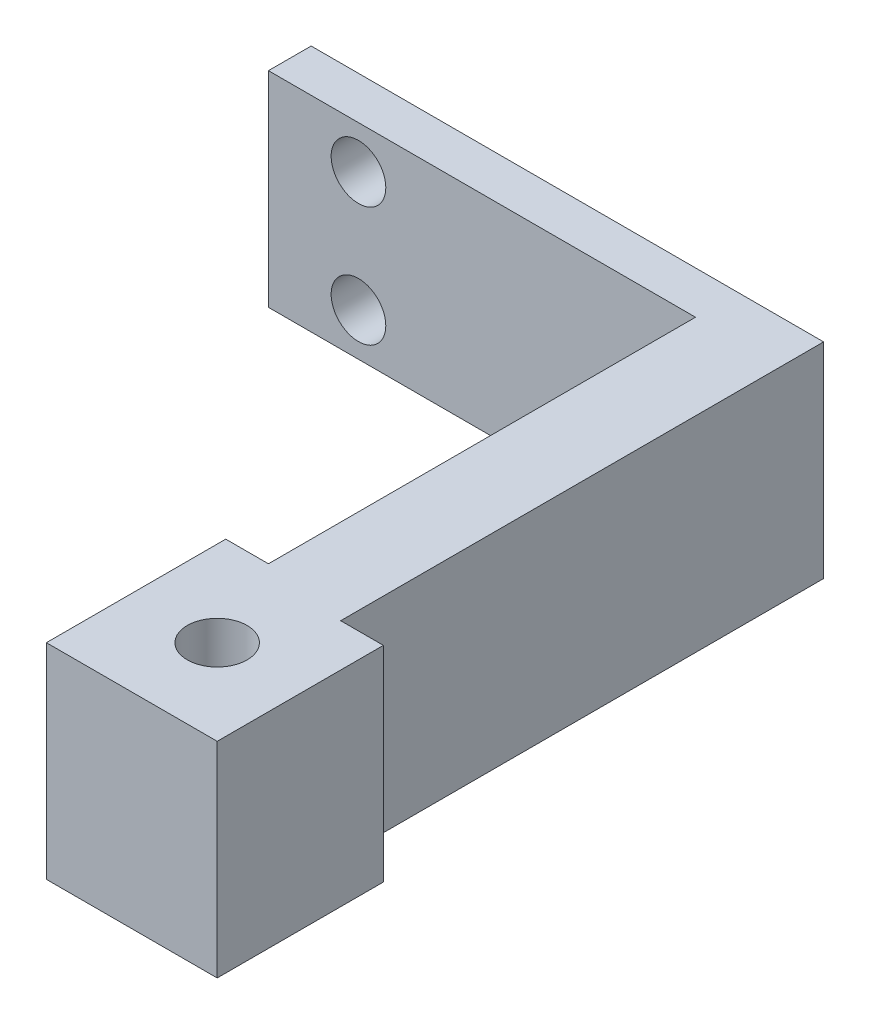
SolidWorks part; units mm, degrees
ref_plane "Front Plane" through (0, 0, 0) normal (0, 0, 1) x (1, 0, 0)
ref_plane "Top Plane" through (0, 0, 0) normal (0, 1, 0) x (1, 0, 0)
ref_plane "Right Plane" through (0, 0, 0) normal (1, 0, 0) x (0, 0, -1)
sketch "Sketch1" plane through (0, 0, 0) normal (0, 1, 0) x (1, 0, 0)
  line L0 (-1.6496, 29.2913) -> (-1.6496, -3.7087)
  line L1 (-1.6496, -3.7087) -> (3.3504, -3.7087)
  line L2 (3.3504, -3.7087) -> (3.3504, 31.7913)
  line L3 (3.3504, 31.7913) -> (-26.6496, 31.7913)
  line L4 (-26.6496, 31.7913) -> (-26.6496, 29.2913)
  line L5 (-26.6496, 29.2913) -> (-1.6496, 29.2913)
  circle A0 centre (0.8504, -1.2087) radius 1.75
  point P8 (0, 0)
  point P9 (0.8504, -3.7087)
  dimension "D3" = 3.5
  dimension "D1" = 2.5
  dimension "D2" = 5
  dimension "D4" = 2.5
  dimension "D5" = 33
  dimension "D6" = 25
extrude "Boss-Extrude1" add sketch "Sketch1" along normal blind 12
sketch "Sketch3" plane through (0, 0, -29.2913) normal (0, 0, 1) x (1, 0, 0)
  line L0 (-21.3798, 9.5) -> (-21.3798, 2.5) construction
  line L1 (-26.6496, 12) -> (-26.6496, 0) construction
  circle A0 centre (-21.3798, 2.5) radius 1.6
  circle A1 centre (-21.3798, 9.5) radius 1.6
  point P4 (0, 0)
  point P7 (-26.6496, 6)
  point P8 (-21.3798, 6)
  dimension "D1" = 3.2
  dimension "D2" = 7
extrude "Cut-Extrude1" cut sketch "Sketch3" against normal through all
sketch "Sketch4" plane through (0, 0, 0) normal (0, 1, 0) x (1, 0, 0)
  line L0 (-1.6496, 4.2913) -> (-4.1496, 4.2913)
  line L1 (-1.6496, 29.2913) -> (-1.6496, -3.7087) construction
  line L2 (-4.1496, 4.2913) -> (-4.1496, -6.2087)
  line L3 (-4.1496, -6.2087) -> (5.8504, -6.2087)
  line L4 (5.8504, -6.2087) -> (5.8504, 3.5191)
  line L5 (5.8504, 3.5191) -> (3.3504, 3.5191)
  line L6 (3.3504, -3.7087) -> (3.3504, 31.7913) construction
  line L7 (3.3504, 3.5191) -> (3.3504, -3.7087)
  line L8 (3.3504, -3.7087) -> (-1.6496, -3.7087)
  line L9 (-1.6496, -3.7087) -> (-1.6496, 4.2913)
  dimension "D1" = 2.5
  dimension "D2" = 2.5
  dimension "D3" = 2.5
  dimension "D4" = 8
extrude "Boss-Extrude2" add sketch "Sketch4" along normal through all
